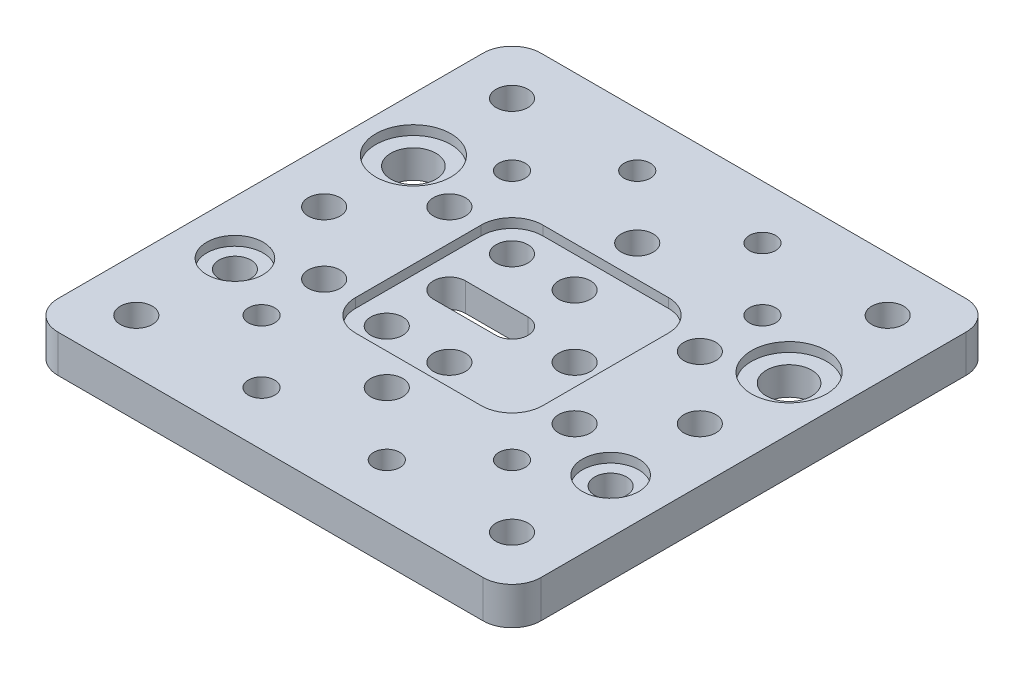
SolidWorks part; units mm, degrees
material "6061-T6 (SS)"
ref_plane "Front Plane" through (0, 0, 0) normal (0, 0, 1) x (1, 0, 0)
ref_plane "Top Plane" through (0, 0, 0) normal (0, 1, 0) x (1, 0, 0)
ref_plane "Right Plane" through (0, 0, 0) normal (1, 0, 0) x (0, 0, -1)
sketch "Sketch1" plane through (0, 0, 0) normal (0, 1, 0) x (1, 0, 0)
  line L0 (-23.7657, 0) -> (0, 0) construction
  line L1 (33.94, -38.575) -> (-33.94, -38.575)
  line L2 (38.575, -33.94) -> (38.575, 33.94)
  line L3 (33.94, 38.575) -> (-33.94, 38.575)
  line L4 (-38.575, -33.94) -> (-38.575, 33.94)
  line L5 (38.575, -38.575) -> (-38.575, 38.575) construction
  line L6 (38.575, 38.575) -> (-38.575, -38.575) construction
  line L7 (0, 0) -> (0, 28.9978) construction
  line L8 (0, 0) -> (-10, 0) construction
  line L9 (0, -2.55) -> (-10, -2.55)
  line L10 (0, 2.55) -> (-10, 2.55)
  arc A0 (-33.94, 38.575) -> (-38.575, 33.94) centre (-33.94, 33.94) ccw
  arc A1 (38.575, 33.94) -> (33.94, 38.575) centre (33.94, 33.94) ccw
  arc A2 (-33.94, -38.575) -> (-38.575, -33.94) centre (-33.94, -33.94) cw
  arc A3 (33.94, -38.575) -> (38.575, -33.94) centre (33.94, -33.94) ccw
  circle A4 centre (-30, 14.25) radius 3.6
  circle A5 centre (-20, 10) radius 2.55
  circle A7 centre (0, 20) radius 2.55
  circle A8 centre (0, 10) radius 2.55
  circle A9 centre (-10, 10) radius 2.55
  circle A11 centre (-30, 30) radius 2.55
  circle A12 centre (-30, 0) radius 2.55
  circle A13 centre (30, 30) radius 2.55
  circle A16 centre (30, 14.25) radius 3.6
  circle A17 centre (30, 0) radius 2.55
  circle A18 centre (20, 10) radius 2.55
  circle A19 centre (20, -10) radius 2.55
  circle A21 centre (-30, -30) radius 2.55
  circle A22 centre (30, -30) radius 2.55
  circle A25 centre (-20, -10) radius 2.55
  circle A27 centre (0, -20) radius 2.55
  circle A28 centre (0, -10) radius 2.55
  circle A29 centre (-10, -10) radius 2.55
  circle A30 centre (10, 0) radius 2.55
  arc A31 (0, -2.55) -> (0, 2.55) centre (0, 0) ccw
  arc A32 (-10, 2.55) -> (-10, -2.55) centre (-10, 0) ccw
  circle A33 centre (30, -14.25) radius 2.55
  circle A34 centre (-30, -14.25) radius 2.55
  point P0 (0, 0)
  point P75 (-5, 0)
  dimension "D2" = 4.635
  dimension "D3" = 5.1
  dimension "D4" = 7.2
  dimension "D12" = 10
  dimension "D1" = 77.15
  dimension "D5" = 40
  dimension "D6" = 60
  dimension "D7" = 40
  dimension "D9" = 20
  dimension "D10" = 28.5
  dimension "D11" = 60
  dimension "D13" = 10
  dimension "D14" = 10
  dimension "D15" = 5.1
extrude "Boss-Extrude1" add sketch "Sketch1" along normal blind 6
hole_wizard "M5x0.8 Tapped Hole1" positions "Sketch4" profile "Sketch3" tap size "M5x0.8" standard "ANSI Metric" end condition through all
sketch "Sketch4" plane through (0, 6, 0) normal (0, 1, 0) x (1, 0, 0)
  line L0 (-17.7377, 0) -> (0, 0) construction
  line L1 (0, 0) -> (0, 30.1375) construction
  point P0 (-20, 20)
  point P2 (-10, 30)
  point P11 (10, 30)
  point P12 (20, 20)
  point P13 (20, -20)
  point P14 (10, -30)
  point P15 (-10, -30)
  point P16 (-20, -20)
  dimension "D1" = 20
  dimension "D2" = 40
  dimension "D3" = 40
  dimension "D4" = 60
sketch "Sketch3" plane through (-20, 6, -20) normal (1, 0, 0) x (0, 0, 1)
  line L0 (0, 0) -> (0, 6)
  line L1 (0, 6) -> (2.1, 6)
  line L2 (2.1, 6) -> (2.1, 0)
  line L5 (2.1, 0) -> (0, 0)
  line L11 (0, -6.35) -> (0, 107.95) construction
  dimension "Thread Major Dia." = 4.2
  dimension "Thru Tap Drill Depth" = 6
sketch "Sketch2" plane through (0, 6, 0) normal (0, 1, 0) x (1, 0, 0)
  line L1 (10.03, -14.95) -> (-10.03, -14.95)
  line L2 (14.95, -10.03) -> (14.95, 10.03)
  line L3 (10.03, 14.95) -> (-10.03, 14.95)
  line L4 (-14.95, -10.03) -> (-14.95, 10.03)
  line L5 (14.95, -14.95) -> (-14.95, 14.95) construction
  line L6 (14.95, 14.95) -> (-14.95, -14.95) construction
  circle A0 centre (-30, 14.25) radius 6
  circle A1 centre (30, 14.25) radius 6
  circle A2 centre (30, -14.25) radius 4.5
  circle A3 centre (-30, -14.25) radius 4.5
  arc A4 (-10.03, 14.95) -> (-14.95, 10.03) centre (-10.03, 10.03) ccw
  arc A5 (10.03, -14.95) -> (14.95, -10.03) centre (10.03, -10.03) ccw
  arc A6 (14.95, 10.03) -> (10.03, 14.95) centre (10.03, 10.03) ccw
  arc A7 (-10.03, -14.95) -> (-14.95, -10.03) centre (-10.03, -10.03) cw
  point P12 (0, 0)
  dimension "D1" = 12
  dimension "D2" = 9
  dimension "D4" = 4.92
  dimension "D3" = 29.9
extrude "Cut-Extrude1" cut sketch "Sketch2" against normal blind 1.5
